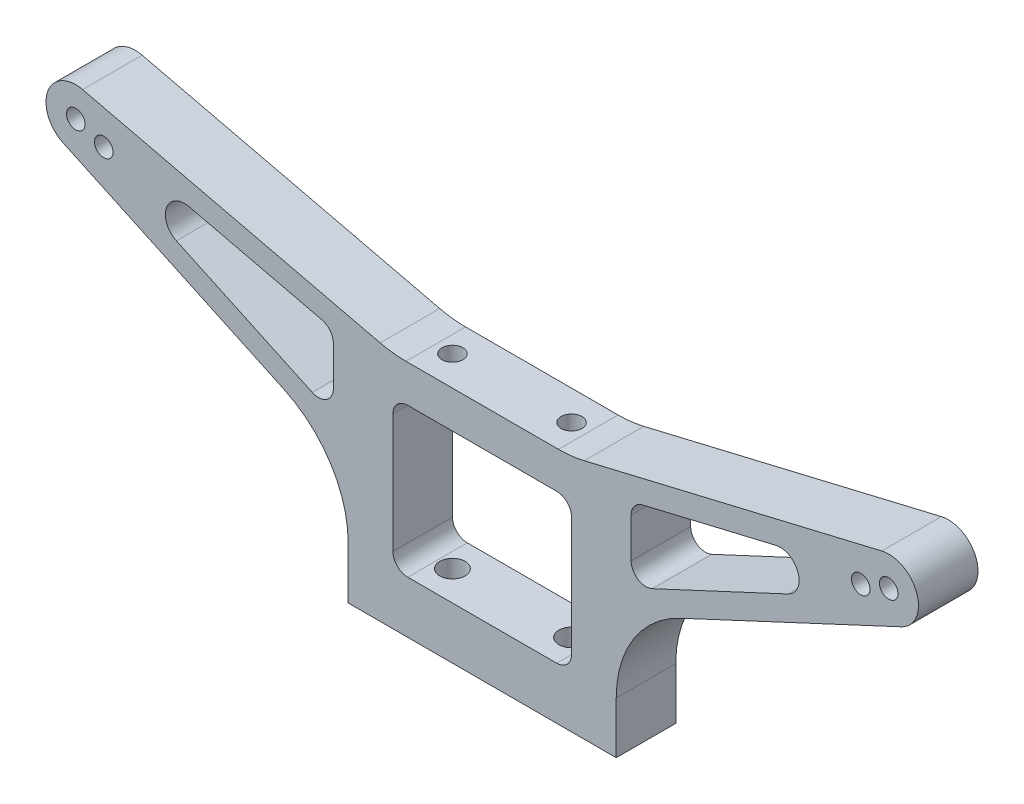
SolidWorks part; units mm, degrees
material "6061 Alloy"
ref_plane "Front Plane" through (0, 0, 0) normal (0, 0, 1) x (1, 0, 0)
ref_plane "Top Plane" through (0, 0, 0) normal (0, 1, 0) x (1, 0, 0)
ref_plane "Right Plane" through (0, 0, 0) normal (1, 0, 0) x (0, 0, -1)
sketch "Sketch2" plane through (0, 0, 0) normal (0, 0, 1) x (1, 0, 0)
  line L0 (18, 0) -> (-18, 0)
  line L1 (-12, 27) -> (12, 27)
  line L2 (-54.6, 38) -> (-24.3895, 38) construction
  line L3 (54.6, 38) -> (24.3895, 38) construction
  line L4 (12, 7) -> (-12, 7)
  line L5 (-12, 7) -> (-12, 27)
  line L6 (53.6763, 41.8919) -> (13.7083, 32.4055)
  line L7 (0, 0) -> (0, 32.9946) construction
  line L8 (18, 6.9636) -> (18, 0)
  line L9 (56.2905, 34.3748) -> (26.6607, 20.5582)
  line L10 (12, 7) -> (12, 27)
  line L11 (-56.2905, 34.3748) -> (-26.6607, 20.5582)
  line L12 (-20, 23.9017) -> (-20, 29.2346)
  line L13 (-21.5381, 31.1805) -> (-39.4068, 35.4217)
  line L14 (-18, 6.9636) -> (-18, 0)
  line L15 (-53.6763, 41.8919) -> (-13.7083, 32.4055)
  line L16 (-10.2443, 32) -> (10.2443, 32)
  line L17 (-22.8452, 22.0891) -> (-41.0855, 30.5947)
  line L18 (20, 23.9017) -> (20, 29.2346)
  line L19 (22.8452, 22.0891) -> (41.0855, 30.5947)
  line L20 (21.5381, 31.1805) -> (39.4068, 35.4217)
  line L21 (-54.6, 38) -> (-17.6498, 24.5512) construction
  circle A0 centre (-54.6, 38) radius 0.5
  arc A1 (26.6607, 20.5582) -> (18, 6.9636) centre (33, 6.9636) ccw
  arc A2 (-53.6763, 41.8919) -> (-56.2905, 34.3748) centre (-54.6, 38) ccw
  arc A3 (-13.7083, 32.4055) -> (-10.2443, 32) centre (-10.2443, 47) ccw
  arc A4 (-26.6607, 20.5582) -> (-18, 6.9636) centre (-33, 6.9636) cw
  arc A5 (13.7083, 32.4055) -> (10.2443, 32) centre (10.2443, 47) cw
  arc A6 (53.6763, 41.8919) -> (56.2905, 34.3748) centre (54.6, 38) cw
  circle A7 centre (54.6, 38) radius 0.5
  arc A8 (-39.4068, 35.4217) -> (-41.0855, 30.5947) centre (-40, 32.9226) ccw
  arc A9 (-20, 29.2346) -> (-21.5381, 31.1805) centre (-22, 29.2346) ccw
  arc A10 (-20, 23.9017) -> (-22.8452, 22.0891) centre (-22, 23.9017) cw
  arc A11 (39.4068, 35.4217) -> (41.0855, 30.5947) centre (40, 32.9226) cw
  arc A12 (20, 23.9017) -> (22.8452, 22.0891) centre (22, 23.9017) ccw
  arc A13 (20, 29.2346) -> (21.5381, 31.1805) centre (22, 29.2346) cw
  circle A14 centre (-50.8412, 36.6319) radius 0.5
  circle A15 centre (50.8412, 36.6319) radius 0.5
  point P3 (-54.6, 38)
  point P21 (0, 7)
  point P28 (0, 32)
  point P31 (0, 27)
  point P33 (18, 16.5196)
  point P36 (12, 32)
  point P38 (-12, 32)
  point P41 (-18, 16.5196)
  dimension "D6" = 1
  dimension "D13" = 15
  dimension "D3" = 4
  dimension "D9" = 2
  dimension "D15" = 40
  dimension "D17" = 4
  dimension "D20" = 1
  dimension "D2" = 54.6
  dimension "D4" = 20
  dimension "D5" = 25
  dimension "D7" = 38
  dimension "D8" = 7
  dimension "D10" = 12
  dimension "D11" = 3
  dimension "D12" = 25
  dimension "D14" = 3
  dimension "D16" = 20
  dimension "D18" = 20
  dimension "D19" = 18
extrude "Base" add sketch "Sketch2" along normal mid plane 8
fillet "Fillet1" radius 2 4 edges at (-12, 7, 0) (12, 7, 0) (12, 27, 0) (-12, 27, 0)
hole_wizard "M3 Clearance Hole1" positions "Sketch5" profile "Sketch6" hole size "M3" standard "ANSI Metric"
sketch "Sketch5" plane through (0, 7, 0) normal (0, 1, 0) x (1, 0, 0)
  line L0 (0, 4) -> (0, -5.3733) construction
  line L1 (-10, 4) -> (10, 4) construction
  line L3 (-29.1636, 0) -> (71.5875, 0) construction
  point P0 (-8, 0)
  point P2 (8, 0)
  point P13 (22, 0)
  point P15 (-22, 0)
  dimension "D1" = 16
  dimension "D2" = 8
  dimension "D3" = 22
  dimension "D4" = 44
sketch "Sketch6" plane through (-8, 7, 0) normal (1, 0, 0) x (0, 0, 1)
  line L0 (0, 0) -> (0, 8.0205)
  line L1 (0, 8.0205) -> (1.7, 6.999)
  line L2 (1.7, 6.999) -> (1.7, 0)
  line L5 (1.7, 0) -> (0, 0)
  line L10 (0, 8.0205) -> (-1.7, 6.999) construction
  line L11 (0, -6.35) -> (0, 107.95) construction
  dimension "Hole Dia." = 3.4
  dimension "Hole Depth" = 6.999
  dimension "Drill Angle" = 118
hole_wizard "Tap Drill for M3x0.5 Tap1" positions "Sketch7" profile "Sketch8" hole size "M3x0.5" standard "ANSI Metric" end condition through all
sketch "Sketch7" plane through (0, 0, 4) normal (0, 0, 1) x (1, 0, 0)
  point P0 (-54.6, 38)
  point P3 (54.6, 38)
  point P4 (-50.8412, 36.6319)
  point P7 (50.8412, 36.6319)
sketch "Sketch8" plane through (-54.6, 38, 4) normal (1, 0, 0) x (0, -1, 0)
  line L0 (0, 0) -> (0, 8)
  line L1 (0, 8) -> (1.25, 8)
  line L2 (1.25, 8) -> (1.25, 0)
  line L5 (1.25, 0) -> (0, 0)
  line L11 (0, -6.35) -> (0, 107.95) construction
  dimension "Thru Hole Dia." = 2.5
  dimension "Thru Hole Depth" = 8
sketch "Sketch10" plane through (0, 32, 0) normal (0, 1, 0) x (1, 0, 0)
  circle A0 centre (-8, 0) radius 1.4
  circle A1 centre (8, 0) radius 1.4
  circle A2 centre (-8, 0) radius 1.7 construction
  circle A3 centre (8, 0) radius 1.7 construction
  dimension "D1" = 2.8
  dimension "D2" = 2.8
extrude "Cut-Extrude1" cut sketch "Sketch10" against normal blind 10
